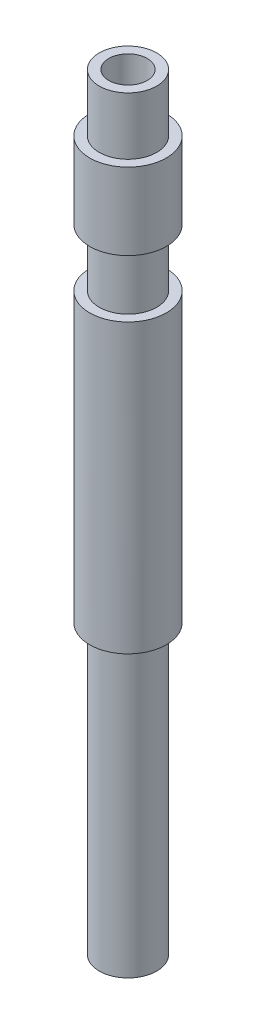
SolidWorks part; units mm, degrees
material "Простая углеродистая сталь"
ref_plane "Спереди" through (0, 0, 0) normal (0, 0, 1) x (1, 0, 0)
ref_plane "Сверху" through (0, 0, 0) normal (0, 1, 0) x (1, 0, 0)
ref_plane "Справа" through (0, 0, 0) normal (1, 0, 0) x (0, 0, -1)
sketch "Эскиз1" plane through (0, 0, 0) normal (0, 1, 0) x (1, 0, 0)
  circle A0 centre (0, 0) radius 1
  circle A1 centre (0, 0) radius 2
  dimension "D1" = 4
  dimension "D2" = 2
extrude "Бобышка-Вытянуть1" add sketch "Эскиз1" along normal blind 40
sketch "Эскиз2" plane through (0, 0, 0) normal (0, 0, 1) x (1, 0, 0)
  line L0 (2, 40) -> (1.5, 40)
  line L1 (2, 40) -> (2, 37)
  line L2 (1.5, 40) -> (1.5, 37)
  line L3 (2, 37) -> (1.5, 37)
  line L4 (2, 33) -> (1.5, 33)
  line L5 (2, 33) -> (2, 30)
  line L6 (1.5, 33) -> (1.5, 30)
  line L7 (2, 30) -> (1.5, 30)
  line L8 (1, 40) -> (-1, 40) construction
  line L9 (1, 40) -> (-1, 40) construction
  line L10 (0, 40) -> (0, 0) construction
  line L11 (-2, 0) -> (2, 0) construction
  line L12 (-2, 0) -> (2, 0) construction
  dimension "D1" = 3
  dimension "D2" = 0.5
  dimension "D3" = 2
  dimension "D4" = 7
revolve "Вырез-Повернуть1" cut sketch "Эскиз2" angle 360 about L10
sketch "Эскиз3" plane through (0, 0, 0) normal (0, 0, 1) x (1, 0, 0)
  line L0 (2, 0) -> (1.5, 0)
  line L1 (2, 0) -> (2, 15)
  line L2 (1.5, 0) -> (1.5, 15)
  line L3 (2, 15) -> (1.5, 15)
  line L4 (2, 30) -> (-2, 30) construction
  line L5 (0, 0) -> (0, 40) construction
  line L6 (1, 40) -> (-1, 40) construction
  line L7 (1, 40) -> (-1, 40) construction
  dimension "D1" = 15
  dimension "D2" = 0.5
revolve "Вырез-Повернуть2" cut sketch "Эскиз3" angle 360 about L5
sketch "Эскиз4" plane through (0, 0, 0) normal (0, 0, 1) x (1, 0, 0)
  line L0 (-2, 20) -> (2, 20) construction
  line L1 (1.5, 40) -> (-1.5, 40) construction
  line L2 (1.5, 40) -> (-1.5, 40) construction
  line L3 (2, 30) -> (-2, 30) construction
  line L4 (2, 30) -> (-2, 30) construction
  line L5 (-2, 30) -> (-2, 15) construction
  line L6 (2, 15) -> (2, 30) construction
  dimension "D1" = 20
ref_plane "Плоскость1" through (0, 20, 0) normal (0, 1, 0) x (1, 0, 0)
sketch "Эскиз5" plane through (0, 20, 0) normal (0, 1, 0) x (1, 0, 0)
  line L0 (-2, 0) -> (2, 0) construction
  circle A0 centre (0, 0) radius 2 construction
